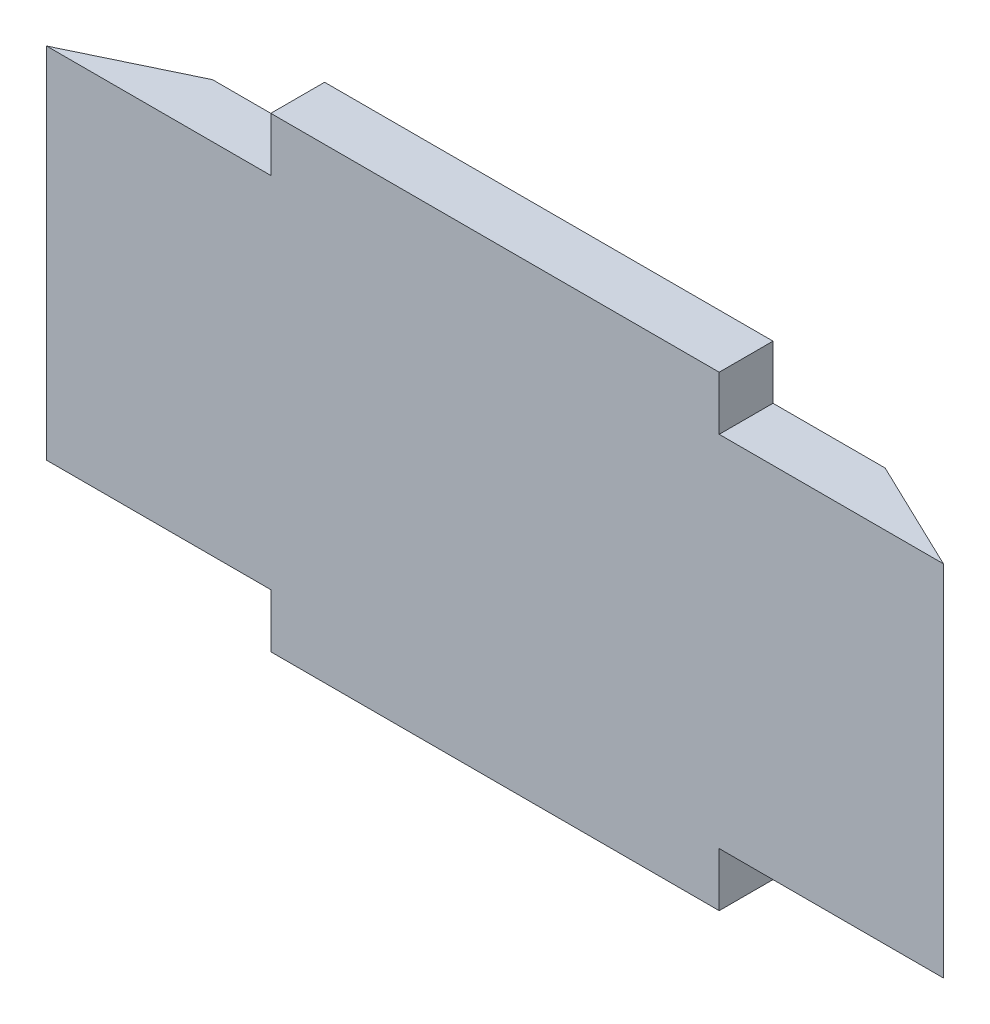
SolidWorks part; units mm, degrees
ref_plane "Plan de face" through (0, 0, 0) normal (0, 0, 1) x (1, 0, 0)
ref_plane "Plan de dessus" through (0, 0, 0) normal (0, 1, 0) x (1, 0, 0)
ref_plane "Plan de droite" through (0, 0, 0) normal (1, 0, 0) x (0, 0, -1)
sketch "Esquisse1" plane through (0, 0, 0) normal (0, 0, 1) x (1, 0, 0)
  line L1 (50, 20) -> (-50, 20)
  line L2 (50, 20) -> (50, -20)
  line L3 (50, -20) -> (-50, -20)
  line L4 (-50, 20) -> (-50, -20)
  line L5 (50, 20) -> (-50, -20) construction
  line L6 (50, -20) -> (-50, 20) construction
  point P0 (0, 0)
  dimension "D1" = 100
  dimension "D2" = 40
extrude "Boss.-Extru.1" add sketch "Esquisse1" along normal blind 6
sketch "Esquisse2" plane through (0, 0, 6) normal (0, 0, 1) x (1, 0, 0)
  line L0 (50, 20) -> (-50, 20) construction
  line L1 (-25, 20) -> (25, 20)
  line L2 (-25, 20) -> (-25, 26)
  line L3 (-25, 26) -> (25, 26)
  line L4 (25, 20) -> (25, 26)
  line L5 (-50, 20) -> (-50, -20) construction
  line L6 (-50, 0) -> (50, 0) construction
  line L7 (50, -20) -> (50, 20) construction
  line L8 (-25, -26) -> (25, -26)
  line L9 (25, -20) -> (25, -26)
  line L10 (-25, -20) -> (25, -20)
  line L11 (-25, -20) -> (-25, -26)
  dimension "D1" = 50
  dimension "D2" = 25
  dimension "D3" = 6
extrude "Boss.-Extru.2" add sketch "Esquisse2" against normal blind 6
sketch "Esquisse3" plane through (0, 20, 0) normal (0, 1, 0) x (1, 0, 0)
  line L0 (-50, -6) -> (-37.5, 0)
  line L1 (-25, 0) -> (-50, 0) construction
  line L2 (-37.5, 0) -> (-50, 0)
  line L3 (-50, 0) -> (-50, -6)
  line L4 (50, -6) -> (37.5, 0)
  line L5 (50, 0) -> (25, 0) construction
  line L6 (37.5, 0) -> (50, 0)
  line L7 (50, 0) -> (50, -6)
extrude "Enlèv. mat.-Extru.1" cut sketch "Esquisse3" against normal through all
